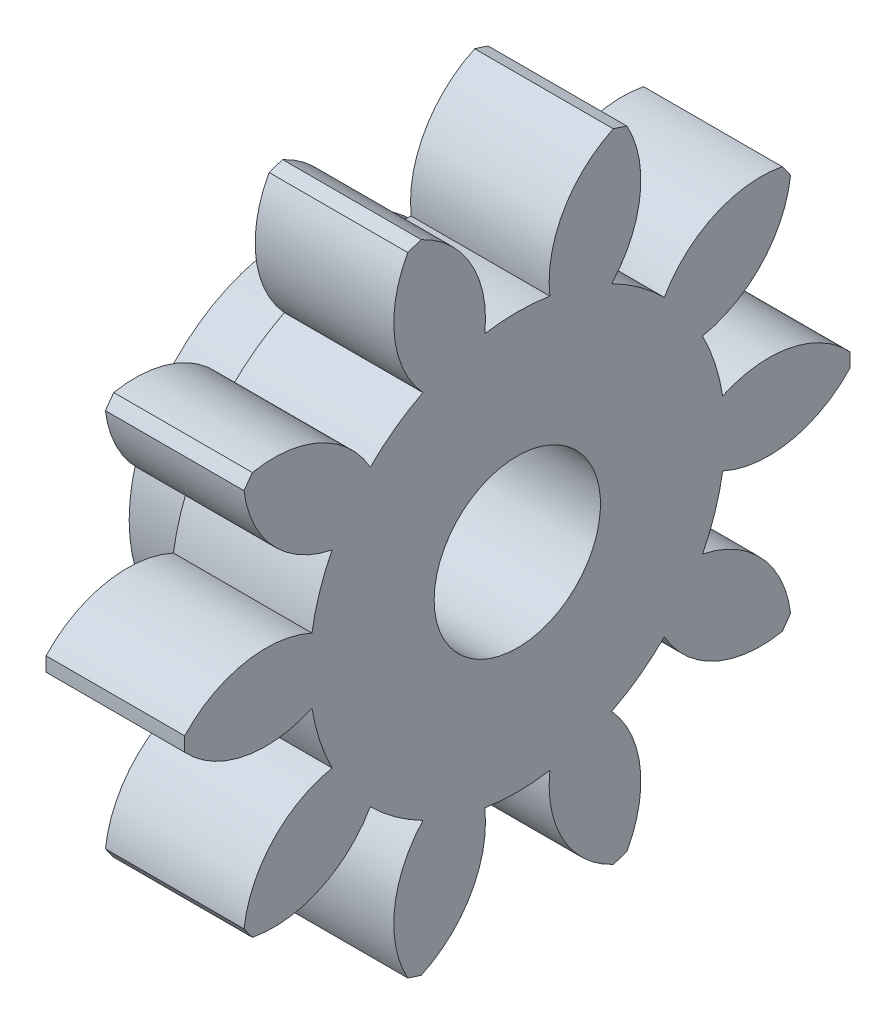
SolidWorks part; units mm, degrees
ref_plane "Plane1" through (0, 0, 0) normal (0, 0, 1) x (1, 0, 0)
ref_plane "Plane2" through (0, 0, 0) normal (0, 1, 0) x (1, 0, 0)
ref_plane "Plane3" through (0, 0, 0) normal (1, 0, 0) x (0, 0, -1)
sketch "HoldingSke" plane through (0, 0, 0) normal (0, 1, 0) x (1, 0, 0)
  line L0 (0, 0) -> (0.4924, -0.0868)
  line L1 (-15, 0) -> (100, 0) construction
  line L2 (0, 0) -> (-2.1039, 2.3779)
  line L3 (0, 0) -> (-11.863, 4.5341)
  line L4 (0, 0) -> (8.5048, 1.4996)
  line L5 (0, 0) -> (-7.4956, -2.7956)
  line L6 (0, 0) -> (-4.1448, -2.7965)
  line L7 (-2.1039, 2.3779) -> (-0.3819, 10.1904)
  line L8 (-76.2, 54.61) -> (-75.2, 54.61)
  line L9 (-71.009, 38.7566) -> (-53.1078, 45.2721)
  line L10 (-76.2, 71.12) -> (104.1128, 71.12)
  line L11 (0, 0) -> (-5, 0)
  line L12 (-76.2, 101.6) -> (-76.133, 101.6)
  line L13 (24.9733, 27.94) -> (52.9518, 28.4284)
  line L14 (24.9733, 27.94) -> (24.9743, 27.94)
  line L15 (24.9733, 27.94) -> (100.4006, 29.5858)
  line L16 (-63.627, -2) -> (-12.827, -2)
  circle A0 centre (0, 0) radius 3
  circle A1 centre (0, 0) radius 6
  circle A2 centre (0, 0) radius 6
  circle A3 centre (0, 0) radius 3
  dimension "MHD" = 12
  dimension "Hub_dia" = 12
  dimension "Bore" = 6
  dimension "MBD" = 6
  dimension "Num_teeth" = 10
  dimension "Pitch" = 0.5
  dimension "Overall_len" = 8
  dimension "Show_teeth" = 10
  dimension "Thickness" = 5
  dimension "OAL" = 8.0001
  dimension "T_dim" = 1
  dimension "Ap" = 20
  dimension "H" = 19.05
  dimension "Pitch_radius" = 180.3128
  dimension "Width" = 5
  dimension "Backlash" = 0.067
  dimension "Addendum_fac" = 1
  dimension "Dedendum_fac" = 1.25
  dimension "Clearance_fac" = 0.25
  dimension "Dedendum_add" = 0.001
  dimension "Module" = 2
sketch "BasProSke" plane through (0, 0, 0) normal (0, 1, 0) x (1, 0, 0)
  line L0 (-10, 0) -> (60, 0) construction
  line L1 (0, 0) -> (0, 12)
  line L2 (0, 0) -> (5, 0)
  line L3 (5, 0) -> (5, 12)
  line L4 (5, 12) -> (0, 12)
  dimension "Thickness" = 5
  dimension "Diameter" = 24
revolve "Base-Revolve" add sketch "BasProSke" angle 360 about L0
sketch "TooCutSke" plane through (0, 0, 0) normal (1, 0, 0) x (0, 0, -1)
  line L1 (0, 0) -> (0, 107) construction
  line L2 (0, 0) -> (-1.6814, 9.8576) construction
  line L3 (0, 0) -> (-6.1153, 18.8209) construction
  line L4 (-1.6814, 9.8576) -> (-3.0576, 9.4105) construction
  arc A0 (1.1737, 7.4066) -> (-1.1737, 7.4066) centre (0, 0) ccw
  arc A1 (3.4979, 11.5054) -> (-3.4979, 11.5054) centre (0, 0) ccw
  circle A2 centre (0, 0) radius 10 construction
  circle A3 centre (0, 0) radius 9.3969 construction
  arc A4 (-1.1737, 7.4066) -> (-3.4979, 11.5054) centre (-5.1477, 7.8615) ccw
  arc A5 (3.4979, 11.5054) -> (1.1737, 7.4066) centre (5.1477, 7.8615) ccw
  dimension "Root_dia" = 14.998
  dimension "Overcut_dia" = 24.0508
  dimension "Pitch_dia" = 20
  dimension "Base_dia" = 18.7939
  dimension "Flank_rad" = 4
  dimension "Half_ang" = 18
  dimension "Half_CT" = 1.4471
extrude "ToothCut" cut sketch "TooCutSke" along normal through all
fillet "Breaks" [suppressed] radius 0.04
fillet "RootFillets" [suppressed] radius 0.501
pattern_circular "TeethCuts" count 10 every 36 about axis through (-10, 0, 0) along (1, 0, 0) of "ToothCut", "RootFillets", "Breaks"
sketch "HubNeaOneSke" plane through (0, 0, 0) normal (-1, 0, 0) x (0, 0, 1)
  circle A0 centre (0, 0) radius 6
  dimension "Diameter" = 12
extrude "HubNearOne" add sketch "HubNeaOneSke" along normal blind 3.0001
sketch "HubNeaBotSke" plane through (0, 0, 0) normal (-1, 0, 0) x (0, 0, 1)
  circle A0 centre (0, 0) radius 6
  dimension "Diameter" = 12
extrude "HubNearBoth" [suppressed] add sketch "HubNeaBotSke" along normal blind 1.5
ref_plane "FarPln" through (5, 0, 0) normal (1, 0, 0) x (0, 0, -1)
sketch "HubFarSke" plane through (5, 0, 0) normal (1, 0, 0) x (0, 0, -1)
  circle A0 centre (0, 0) radius 6
  dimension "Diameter" = 12
extrude "HubFar" [suppressed] add sketch "HubFarSke" along normal blind 1.5
sketch "BorSke" plane through (0, 0, 0) normal (1, 0, 0) x (0, 0, -1)
  circle A0 centre (0, 0) radius 3
  dimension "Diameter" = 6
extrude "Bore" cut sketch "BorSke" along normal mid plane 16.0001
sketch "KeySke" plane through (0, 0, 0) normal (1, 0, 0) x (0, 0, -1)
  line L0 (-1, 0) -> (-1, 4)
  line L1 (-1, 4) -> (1, 4)
  line L2 (1, 4) -> (1, 0)
  line L3 (0, 0) -> (0, 34) construction
  line L4 (-1, 0) -> (1, 0)
  dimension "Offset" = 4
  dimension "Width" = 2
extrude "Keyway" [suppressed] cut sketch "KeySke" along normal mid plane 16.0001
pattern_circular "Keyway2" [suppressed] count 2 every 90 about axis through (-10, 0, 0) along (1, 0, 0)
sketch "Sketch1" plane through (-3.0001, 0, 0) normal (-1, 0, 0) x (0, 0, 1)
  circle A0 centre (0, 0) radius 3.5
  circle A1 centre (0, 0) radius 3 construction
  circle M1 centre (0, 0) radius 3
  dimension "D1" = 0.5
extrude "Cut-Extrude1" cut sketch "Sketch1" against normal blind 1 contours A0 M1
equation "' \"Module@HoldingSke\" = 6.35"
equation "' \"Num_teeth@HoldingSke\" = 12"
equation "' \"Ap@HoldingSke\" =  20"
equation "' \"Ap@HoldingSke\" = 20"
equation "' \"Width@HoldingSke\" = 0.5 * 25.4"
equation "' \"Hub_dia@HoldingSke\"= 1 * 25.4"
equation "' \"Hub_dia@HoldingSke\" = 1 * 25.4"
equation "' \"Overall_len@HoldingSke\" = 1.0 * 25.4"
equation "' \"Bore@HoldingSke\" = 0.75 * 25.4"
equation "' \"T_dim@HoldingSke\" = 0.1 * 25.4"
equation "' \"Width@KeySke\" = 0.25 * 25.4"
equation "' \"Show_teeth@HoldingSke\" = 13"
equation "' \"Backlash@HoldingSke\" = 0.009 * 25.4"
equation "' \"Addendum_fac@HoldingSke\" = 1.0"
equation "' \"Dedendum_fac@HoldingSke\" = 1.25"
equation "' \"Dedendum_add@HoldingSke\" = 0.00005 * 25.4"
equation "' \"Clearance_fac@HoldingSke\" = 0.25"
equation "\"Pitch@HoldingSke\" = 1 / \"Module@HoldingSke\""
equation "\"Overcut_dia@TooCutSke\" = (\"Num_teeth@HoldingSke\" + 2 * \"Addendum_fac@HoldingSke\") / \"Pitch@HoldingSke\" + 0.002 * 25.4"
equation "\"Pitch_dia@TooCutSke\" = \"Num_teeth@HoldingSke\" / \"Pitch@HoldingSke\""
equation "\"Base_dia@TooCutSke\" = \"Num_teeth@HoldingSke\" / \"Pitch@HoldingSke\" * cos((\"Ap@HoldingSke\"  * 3.14159265 / 180))"
equation "\"Root_dia@TooCutSke\" = (\"Num_teeth@HoldingSke\" + 2) / \"Pitch@HoldingSke\" - 2 * (\"Addendum_fac@HoldingSke\" + \"Dedendum_fac@HoldingSke\") / \"Pitch@HoldingSke\" - \"Dedendum_add@HoldingSke\" * 2"
equation "\"Half_ang@TooCutSke\" = 180 / \"Num_teeth@HoldingSke\""
equation "\"Half_CT@TooCutSke\" = \"Num_teeth@HoldingSke\" / \"Pitch@HoldingSke\" * sin((3.14159265 / 2 / \"Num_teeth@HoldingSke\")) / 2 - 7 * \"Backlash@HoldingSke\" / 4"
equation "\"Flank_rad@TooCutSke\" = \"Num_teeth@HoldingSke\" / \"Pitch@HoldingSke\" / 5"
equation "\"Radius@RootFillets\" = \"Clearance_fac@HoldingSke\" / \"Pitch@HoldingSke\" + \"Dedendum_add@HoldingSke\""
equation "\"Break_rad@Breaks\" = 0.02 / \"Pitch@HoldingSke\""
equation "\"Thickness@HoldingSke\" = \"Width@HoldingSke\""
equation "\"OAL@HoldingSke\" = \"Thickness@HoldingSke\""
equation "\"MHD@HoldingSke\" = (\"Num_teeth@HoldingSke\" + 2) / \"Pitch@HoldingSke\" - 2 * (\"Addendum_fac@HoldingSke\" + \"Dedendum_fac@HoldingSke\")  / \"Pitch@HoldingSke\" - \"Dedendum_add@HoldingSke\" * 2"
equation "\"MBD@HoldingSke\" = (\"Num_teeth@HoldingSke\" + 2) / \"Pitch@HoldingSke\" - 2 * (\"Addendum_fac@HoldingSke\" + \"Dedendum_fac@HoldingSke\")  / \"Pitch@HoldingSke\" - \"Dedendum_add@HoldingSke\" * 2 - 0.002 * 25.4"
equation "\"MHD@HoldingSke\" = ((sgn( \"MHD@HoldingSke\" - \"Hub_dia@HoldingSke\" )-1)*( \"MHD@HoldingSke\" - \"Hub_dia@HoldingSke\" ))/-2+ \"Hub_dia@HoldingSke\""
equation "\"MBD@HoldingSke\" = ((sgn( \"MBD@HoldingSke\" - \"Bore@HoldingSke\" )-1)*( \"MBD@HoldingSke\" - \"Bore@HoldingSke\" ))/-2+ \"Bore@HoldingSke\""
equation "\"OAL@HoldingSke\" = ((sgn( \"OAL@HoldingSke\" - \"Overall_len@HoldingSke\" )+1)*( \"OAL@HoldingSke\" - \"Overall_len@HoldingSke\" ))/2 + \"Overall_len@HoldingSke\" + 0.000002 * 25.4"
equation "\"Num_teeth@TeethCuts\" = int( \"Show_teeth@HoldingSke\" ) + 1"
equation "\"Num_teeth@TeethCuts\" = ((sgn( \"Num_teeth@TeethCuts\" - \"Num_teeth@HoldingSke\" )-1)*( \"Num_teeth@TeethCuts\" - \"Num_teeth@HoldingSke\" ))/-2+ \"Num_teeth@HoldingSke\""
equation "\"Num_teeth@TeethCuts\" = ((sgn( \"Num_teeth@TeethCuts\" - 2.0)+1)*( \"Num_teeth@TeethCuts\" - 2.0))/2 +2.0"
equation "\"Angle@TeethCuts\" = 360.0 / \"Num_teeth@HoldingSke\""
equation "\"Diameter@BasProSke\" = (\"Num_teeth@HoldingSke\" + 2 * \"Addendum_fac@HoldingSke\") / \"Pitch@HoldingSke\""
equation "\"Thickness@BasProSke\"  = \"Thickness@HoldingSke\""
equation "' \"Fillet_rad@BasProSke\" =  \"Thickness@HoldingSke\" * 0.05"
equation "' \"Fillet_rad@BasProSke\" = \"Thickness@HoldingSke\" * 0.05"
equation "\"MHD@HoldingSke\" = ((sgn( \"MHD@HoldingSke\" - \"Root_dia@TooCutSke\" )-1)*( \"MHD@HoldingSke\" - \"Root_dia@TooCutSke\" ))/-2+ \"Root_dia@TooCutSke\""
equation "\"Diameter@HubNeaOneSke\" = \"MHD@HoldingSke\""
equation "\"Length@HubNearOne\" = \"OAL@HoldingSke\" - \"Thickness@BasProSke\""
equation "\"Diameter@HubNeaBotSke\" = \"MHD@HoldingSke\""
equation "\"Length@HubNearBoth\" = ( \"OAL@HoldingSke\" - \"Thickness@BasProSke\" ) / 2.0"
equation "\"Thickness@FarPln\" = \"Thickness@BasProSke\""
equation "\"Diameter@HubFarSke\" = \"MHD@HoldingSke\""
equation "\"Length@HubFar\" = ( \"OAL@HoldingSke\" - \"Thickness@BasProSke\" ) / 2.0"
equation "\"Diameter@BorSke\" = \"MBD@HoldingSke\""
equation "\"D1@Bore\" = \"OAL@HoldingSke\" * 2.0"
equation "\"D1@Keyway\" = \"OAL@HoldingSke\" * 2.0"
equation "\"Offset@KeySke\" = \"T_dim@HoldingSke\" + \"MBD@HoldingSke\" / 2.0"
